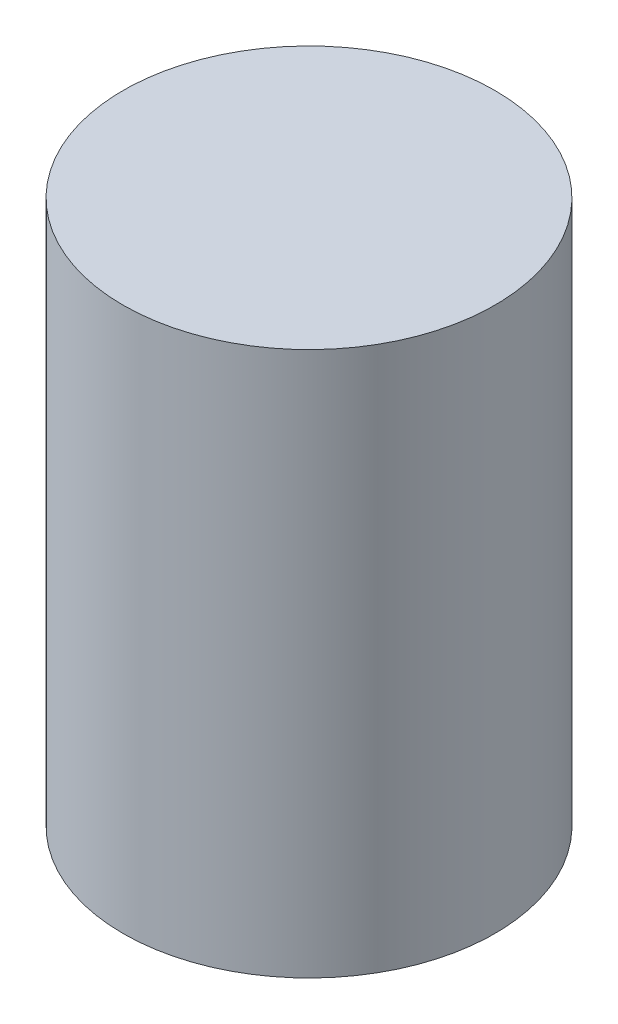
SolidWorks part; units mm, degrees
ref_plane "Front Plane" through (0, 0, 0) normal (0, 0, 1) x (1, 0, 0)
ref_plane "Top Plane" through (0, 0, 0) normal (0, 1, 0) x (1, 0, 0)
ref_plane "Right Plane" through (0, 0, 0) normal (1, 0, 0) x (0, 0, -1)
sketch "Sketch1" plane through (0, 0, 0) normal (0, 1, 0) x (1, 0, 0)
  line L0 (284.2974, 199.1145) -> (335.6873, 199.1145) construction
  line L1 (-27.4588, 43.4177) -> (32.5412, 43.4177)
  line L2 (32.5412, 43.4177) -> (32.5412, -16.3494)
  line L3 (32.5412, -16.3494) -> (-27.4588, -16.3494)
  line L4 (-27.4588, -16.3494) -> (-27.4588, 43.4177)
  circle A0 centre (2.6009, 13.789) radius 20.5
  dimension "D2" = 41
  dimension "D1" = 60
extrude "Boss-Extrude1" add sketch "Sketch1" along normal blind 60 contours A0
